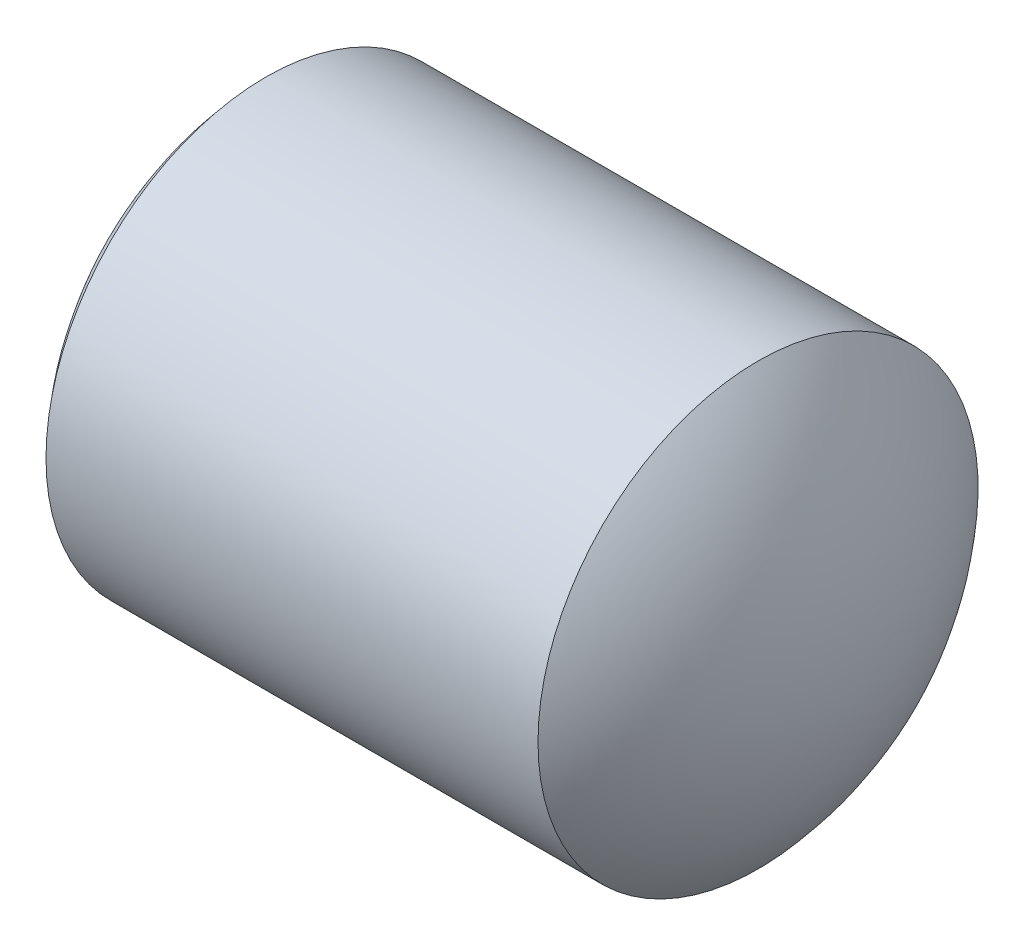
SolidWorks part; units mm, degrees
ref_plane "前视基准面" through (0, 0, 0) normal (0, 0, 1) x (1, 0, 0)
ref_plane "上视基准面" through (0, 0, 0) normal (0, 1, 0) x (1, 0, 0)
ref_plane "右视基准面" through (0, 0, 0) normal (1, 0, 0) x (0, 0, -1)
sketch "草图1" plane through (0, 0, 0) normal (0, 0, 1) x (1, 0, 0)
  line L5 (232.2485, 133.3449) -> (235.7234, 133.3449) construction
  line L6 (232.872, 134.3449) -> (235.1081, 134.3449)
  line L8 (235.1081, 132.3449) -> (232.872, 132.3449)
  arc A0 (232.872, 134.3449) -> (232.872, 132.3449) centre (233.99, 133.3449) ccw
  arc A1 (235.1081, 132.3449) -> (235.1081, 134.3449) centre (233.99, 133.3449) ccw
  dimension "D1" = 2
  dimension "D2" = 1.5
revolve "旋转1" add sketch "草图1" angle 360 about L5
